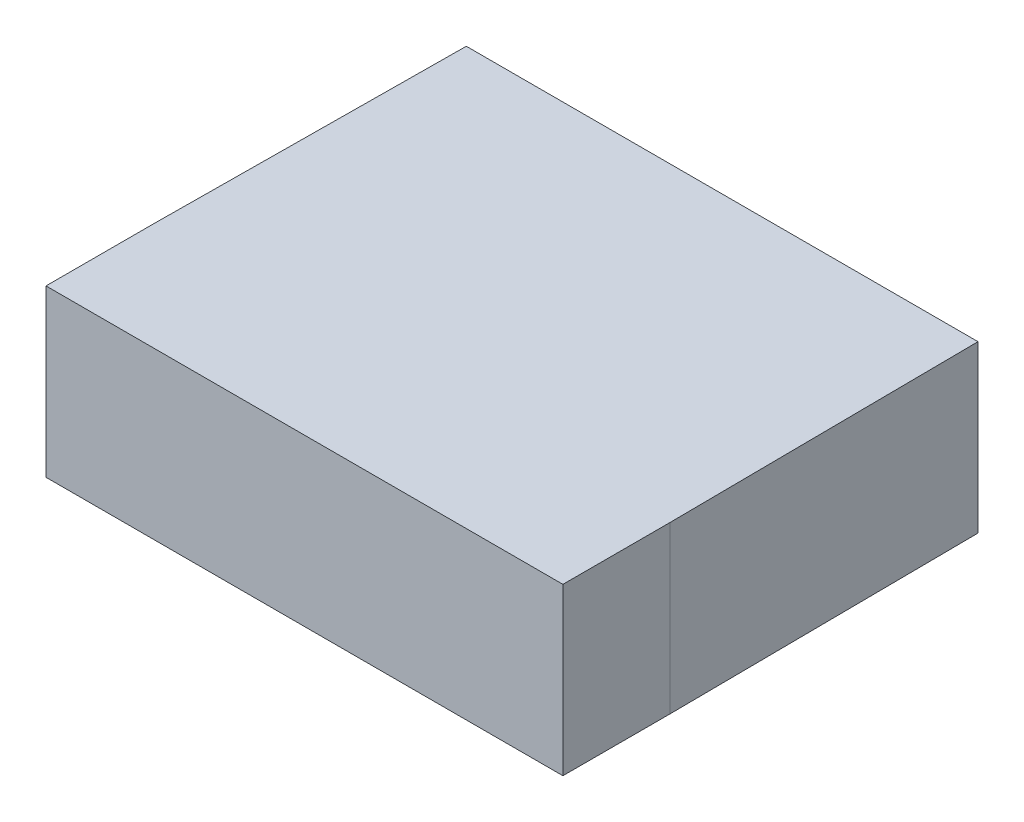
SolidWorks part; units mm, degrees
ref_plane "Front Plane" through (0, 0, 0) normal (0, 0, 1) x (1, 0, 0)
ref_plane "Top Plane" through (0, 0, 0) normal (0, 1, 0) x (1, 0, 0)
ref_plane "Right Plane" through (0, 0, 0) normal (1, 0, 0) x (0, 0, -1)
sketch "Sketch1" plane through (0, 0, 0) normal (0, 1, 0) x (1, 0, 0)
  line L0 (-4.9, 0) -> (4.9, 0)
  line L1 (4.9, 0) -> (4.95, -5.95)
  line L2 (4.95, -5.95) -> (4.95, -8)
  line L3 (4.95, -8) -> (-4.95, -8)
  line L4 (-4.95, -8) -> (-4.95, -5.95)
  line L5 (-4.95, -5.95) -> (-4.9, 0)
  point P9 (0, -8)
  point P10 (0, 0)
  dimension "D1" = 9.8
  dimension "D2" = 9.9
  dimension "D3" = 5.95
  dimension "D4" = 8
extrude "Boss-Extrude1" add sketch "Sketch1" along normal blind 3.175
equation "\"bottomThickness\"= .220in"
equation "\"wallThickness\"= .125in"
equation "\"D1@Boss-Extrude1\"=\"wallThickness\""
